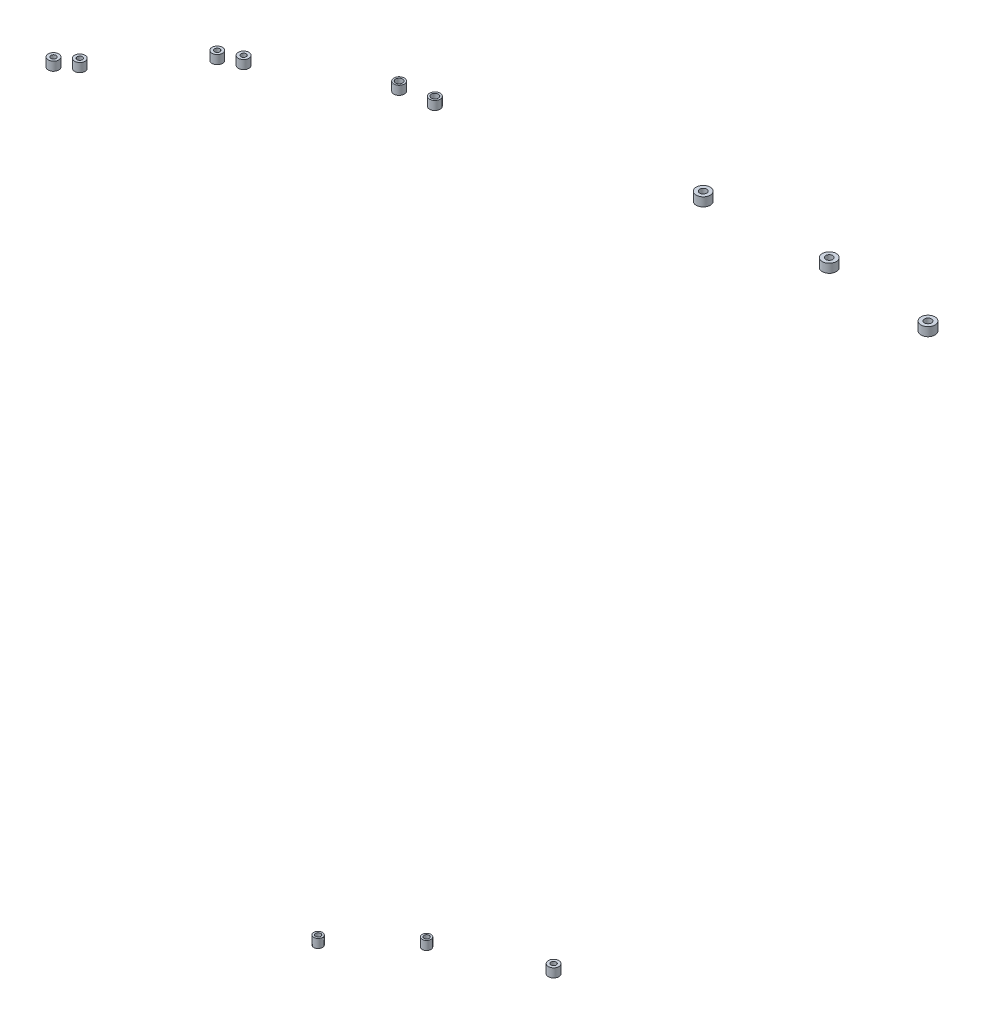
SolidWorks part; units mm, degrees
material "ABS"
ref_plane "Płaszczyzna XY" through (0, 0, 0) normal (0, 0, 1) x (1, 0, 0)
ref_plane "Płaszczyzna XZ" through (0, 0, 0) normal (0, 1, 0) x (1, 0, 0)
ref_plane "Płaszczyzna YZ" through (0, 0, 0) normal (1, 0, 0) x (0, 0, -1)
sketch "Szkic1" plane through (0, 700, 0) normal (0, 1, 0) x (1, 0, 0)
  circle A0 centre (-474.4468, -382.6878) radius 3 construction
  circle A1 centre (-466.3081, -375.8594) radius 3 construction
  circle A2 centre (-431.0397, -332.7742) radius 3 construction
  circle A3 centre (-421.0901, -327.7251) radius 3 construction
  circle A4 centre (-364.0511, -296.1018) radius 3 construction
  circle A5 centre (-346.3899, -293.3962) radius 3 construction
  circle A6 centre (-223.0248, -263.8022) radius 4 construction
  circle A7 centre (-154.3447, -260.6438) radius 4 construction
  circle A8 centre (-94.9095, -263.8022) radius 4 construction
  circle A9 centre (-474.4468, -382.6878) radius 3
  circle A10 centre (-466.3081, -375.8594) radius 3
  circle A11 centre (-431.0397, -332.7742) radius 3
  circle A12 centre (-421.0901, -327.7251) radius 3
  circle A13 centre (-364.0511, -296.1018) radius 3
  circle A14 centre (-346.3899, -293.3962) radius 3
  circle A15 centre (-223.0248, -263.8022) radius 4
  circle A16 centre (-154.3447, -260.6438) radius 4
  circle A17 centre (-94.9095, -263.8022) radius 4
  circle A18 centre (-474.4468, -382.6878) radius 1.5 construction
  circle A19 centre (-466.3081, -375.8594) radius 1.5 construction
  circle A20 centre (-431.0397, -332.7742) radius 1.5 construction
  circle A21 centre (-421.0901, -327.7251) radius 1.5 construction
  circle A22 centre (-364.0511, -296.1018) radius 2 construction
  circle A23 centre (-346.3899, -293.3962) radius 2 construction
  circle A24 centre (-223.0248, -263.8022) radius 2 construction
  circle A25 centre (-154.3447, -260.6438) radius 2 construction
  circle A26 centre (-94.9095, -263.8022) radius 2 construction
  circle A27 centre (-474.4468, -382.6878) radius 1.5
  circle A28 centre (-466.3081, -375.8594) radius 1.5
  circle A29 centre (-431.0397, -332.7742) radius 1.5
  circle A30 centre (-421.0901, -327.7251) radius 1.5
  circle A31 centre (-364.0511, -296.1018) radius 2
  circle A32 centre (-346.3899, -293.3962) radius 2
  circle A33 centre (-223.0248, -263.8022) radius 2
  circle A34 centre (-154.3447, -260.6438) radius 2
  circle A35 centre (-94.9095, -263.8022) radius 2
extrude "Dodanie-wyciągnięcie1" add sketch "Szkic1" along normal blind 5
sketch "Szkic2" plane through (0, 294.7, 0) normal (0, -1, 0) x (1, 0, 0)
  circle A0 centre (-370.9569, 335.3671) radius 2.5 construction
  circle A1 centre (-289.6871, 282.4241) radius 3 construction
  circle A2 centre (-339.083, 305.4298) radius 2.5 construction
  circle A3 centre (-370.9569, 335.3671) radius 2.5
  circle A4 centre (-289.6871, 282.4241) radius 3
  circle A5 centre (-339.083, 305.4298) radius 2.5
  circle A6 centre (-370.9569, 335.3671) radius 1.5
  circle A7 centre (-339.083, 305.4298) radius 1.5
  circle A8 centre (-289.6871, 282.4241) radius 1.5
  dimension "D1" = 3
  dimension "D2" = 3
  dimension "D3" = 3
extrude "Dodanie-wyciągnięcie2" add sketch "Szkic2" against normal blind 5 separate body
